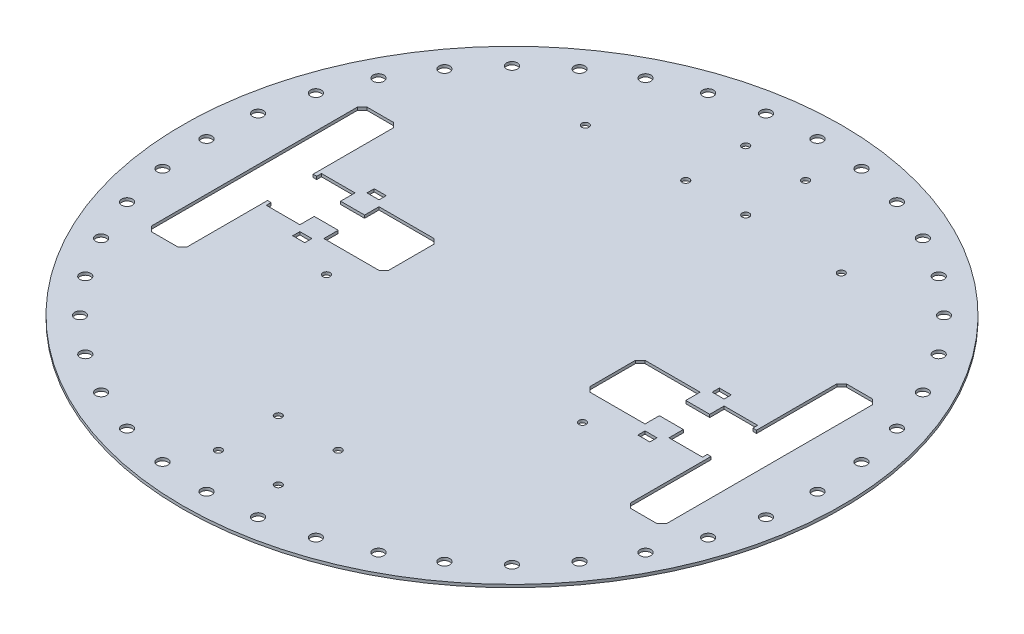
SolidWorks part; units mm, degrees
ref_plane "Front Plane" through (0, 0, 0) normal (0, 0, 1) x (1, 0, 0)
ref_plane "Top Plane" through (0, 0, 0) normal (0, 1, 0) x (1, 0, 0)
ref_plane "Right Plane" through (0, 0, 0) normal (1, 0, 0) x (0, 0, -1)
sketch "Sketch1" plane through (0, 0, 0) normal (0, 1, 0) x (1, 0, 0)
  circle A0 centre (0, 0) radius 137.5
  dimension "D1" = 275
extrude "Boss-Extrude1" add sketch "Sketch1" along normal blind 1.2
sketch "Sketch3" plane through (0, 1.2, 0) normal (0, 1, 0) x (1, 0, 0)
  line L0 (0, 127.4549) -> (0, 0) construction
  line L1 (0, 0) -> (19.9383, 125.8858) construction
  line L2 (39.3857, 121.2169) -> (0, 0) construction
  circle A0 centre (0, 127.4549) radius 2.25
  circle A2 centre (19.9383, 125.8858) radius 2.25
  circle A3 centre (39.3857, 121.2169) radius 2.25
  circle A4 centre (57.8633, 113.5632) radius 2.25
  circle A5 centre (74.9161, 103.1132) radius 2.25
  circle A6 centre (90.1243, 90.1243) radius 2.25
  circle A7 centre (103.1132, 74.9161) radius 2.25
  circle A8 centre (113.5632, 57.8633) radius 2.25
  circle A9 centre (121.2169, 39.3857) radius 2.25
  circle A10 centre (125.8858, 19.9383) radius 2.25
  circle A11 centre (127.4549, 0) radius 2.25
  circle A12 centre (125.8858, -19.9383) radius 2.25
  circle A13 centre (121.2169, -39.3857) radius 2.25
  circle A14 centre (113.5632, -57.8633) radius 2.25
  circle A15 centre (103.1132, -74.9161) radius 2.25
  circle A16 centre (90.1243, -90.1243) radius 2.25
  circle A17 centre (74.9161, -103.1132) radius 2.25
  circle A18 centre (57.8633, -113.5632) radius 2.25
  circle A19 centre (39.3857, -121.2169) radius 2.25
  circle A20 centre (19.9383, -125.8858) radius 2.25
  circle A21 centre (0, -127.4549) radius 2.25
  circle A22 centre (-19.9383, -125.8858) radius 2.25
  circle A23 centre (-39.3857, -121.2169) radius 2.25
  circle A24 centre (-57.8633, -113.5632) radius 2.25
  circle A25 centre (-74.9161, -103.1132) radius 2.25
  circle A26 centre (-90.1243, -90.1243) radius 2.25
  circle A27 centre (-103.1132, -74.9161) radius 2.25
  circle A28 centre (-113.5632, -57.8633) radius 2.25
  circle A29 centre (-121.2169, -39.3857) radius 2.25
  circle A30 centre (-125.8858, -19.9383) radius 2.25
  circle A31 centre (-127.4549, 0) radius 2.25
  circle A32 centre (-125.8858, 19.9383) radius 2.25
  circle A33 centre (-121.2169, 39.3857) radius 2.25
  circle A34 centre (-113.5632, 57.8633) radius 2.25
  circle A35 centre (-103.1132, 74.9161) radius 2.25
  circle A36 centre (-90.1243, 90.1243) radius 2.25
  circle A37 centre (-74.9161, 103.1132) radius 2.25
  circle A38 centre (-57.8633, 113.5632) radius 2.25
  circle A39 centre (-39.3857, 121.2169) radius 2.25
  circle A40 centre (-19.9383, 125.8858) radius 2.25
  dimension "D1" = 4.5
  dimension "D2" = 40
  dimension "D3" = 20
extrude "Cut-Extrude1" cut sketch "Sketch3" against normal through all
sketch "Sketch4" plane through (0, 1.2, 0) normal (0, 1, 0) x (1, 0, 0)
  line L0 (0, 137.5) -> (0, -137.5) construction
  line L1 (-137.5, 0) -> (137.5, 0) construction
  line L2 (-107.5, -43) -> (-107.5, 43)
  line L3 (-105.5, 45) -> (-94.5, 45)
  line L4 (-92.5, 43) -> (-92.5, 9.5)
  line L5 (-92.5, 9.5) -> (-91, 9.5)
  line L6 (-91, 9.5) -> (-91, 11.5)
  line L7 (-91, 11.5) -> (-77, 11.5)
  line L8 (-77, 11.5) -> (-77, 5.5)
  line L9 (-77, 5.5) -> (-67, 5.5)
  line L10 (-67, 5.5) -> (-67, 11.5)
  line L11 (-67, 11.5) -> (-44, 11.5)
  line L12 (-42, 9.5) -> (-42, -9.5)
  line L13 (-67, -11.5) -> (-44, -11.5)
  line L14 (-67, -5.5) -> (-67, -11.5)
  line L15 (-77, -5.5) -> (-67, -5.5)
  line L16 (-77, -11.5) -> (-77, -5.5)
  line L17 (-91, -11.5) -> (-77, -11.5)
  line L18 (-91, -9.5) -> (-91, -11.5)
  line L19 (-92.5, -9.5) -> (-91, -9.5)
  line L20 (-92.5, -43) -> (-92.5, -9.5)
  line L21 (-105.5, -45) -> (-94.5, -45)
  line L22 (-44, 11.5) -> (-42, 9.5)
  line L23 (-44, -11.5) -> (-42, -9.5)
  line L24 (-107.5, 43) -> (-105.5, 45)
  line L25 (-94.5, 45) -> (-92.5, 43)
  line L26 (-107.5, -43) -> (-105.5, -45)
  line L27 (-94.5, -45) -> (-92.5, -43)
  line L28 (94.5, -45) -> (92.5, -43)
  line L29 (107.5, -43) -> (105.5, -45)
  line L30 (94.5, 45) -> (92.5, 43)
  line L31 (107.5, 43) -> (105.5, 45)
  line L32 (44, -11.5) -> (42, -9.5)
  line L33 (44, 11.5) -> (42, 9.5)
  line L34 (105.5, -45) -> (94.5, -45)
  line L35 (92.5, -43) -> (92.5, -9.5)
  line L36 (92.5, -9.5) -> (91, -9.5)
  line L37 (91, -9.5) -> (91, -11.5)
  line L38 (91, -11.5) -> (77, -11.5)
  line L39 (77, -11.5) -> (77, -5.5)
  line L40 (77, -5.5) -> (67, -5.5)
  line L41 (67, -5.5) -> (67, -11.5)
  line L42 (67, -11.5) -> (44, -11.5)
  line L43 (42, 9.5) -> (42, -9.5)
  line L44 (67, 11.5) -> (44, 11.5)
  line L45 (67, 5.5) -> (67, 11.5)
  line L46 (77, 5.5) -> (67, 5.5)
  line L47 (77, 11.5) -> (77, 5.5)
  line L48 (91, 11.5) -> (77, 11.5)
  line L49 (91, 9.5) -> (91, 11.5)
  line L50 (92.5, 9.5) -> (91, 9.5)
  line L51 (92.5, 43) -> (92.5, 9.5)
  line L52 (105.5, 45) -> (94.5, 45)
  line L53 (107.5, -43) -> (107.5, 43)
  circle A2 centre (0, 0) radius 137.5 construction
  point P8 (-107.5, 45)
  point P9 (-42, -11.5)
  point P10 (-92.5, 45)
  point P18 (-42, 11.5)
  point P27 (-92.5, -45)
  point P28 (-107.5, -45)
  point P29 (-100, 0)
  point P39 (-100, 45)
  point P68 (100, 0)
  point P69 (107.5, -45)
  point P70 (92.5, -45)
  point P71 (42, 11.5)
  point P72 (92.5, 45)
  point P73 (42, -11.5)
  point P74 (107.5, 45)
  dimension "D1" = 90
  dimension "D2" = 15
  dimension "D3" = 100
  dimension "D4" = 1.5
  dimension "D5" = 2
  dimension "D6" = 14
  dimension "D7" = 23
  dimension "D8" = 6
  dimension "D9" = 10
  dimension "D10" = 35
extrude "Cut-Extrude2" cut sketch "Sketch4" against normal blind 1.2
sketch "Sketch5" plane through (0, 1.2, 0) normal (0, 1, 0) x (1, 0, 0)
  line L0 (0, 30) -> (0, 0) construction
  line L1 (-53.4, 84) -> (53.4, 84) construction
  line L2 (-53.4, 84) -> (-53.4, -24) construction
  line L3 (-53.4, -24) -> (53.4, -24) construction
  line L4 (53.4, 84) -> (53.4, -24) construction
  line L5 (-53.4, 84) -> (53.4, -24) construction
  line L6 (-53.4, -24) -> (53.4, 84) construction
  circle A0 centre (-53.4, 84) radius 1.5
  circle A1 centre (53.4, 84) radius 1.5
  circle A2 centre (53.4, -24) radius 1.5
  circle A3 centre (-53.4, -24) radius 1.5
  point P0 (0, 30)
  dimension "D3" = 3
  dimension "D1" = 106.8
  dimension "D2" = 108
  dimension "D4" = 30
extrude "Cut-Extrude3" cut sketch "Sketch5" against normal through all
sketch "Sketch6" plane through (0, 1.2, 0) normal (0, 1, 0) x (1, 0, 0)
  line L0 (-137.5, 0) -> (137.5, 0) construction
  line L1 (0, 137.5) -> (0, -137.5) construction
  line L2 (-12.5, -85) -> (12.5, -110) construction
  line L3 (-12.5, 110) -> (12.5, 110) construction
  line L4 (-12.5, 110) -> (-12.5, 85) construction
  line L5 (-12.5, 85) -> (12.5, 85) construction
  line L6 (12.5, 110) -> (12.5, 85) construction
  line L7 (-12.5, 110) -> (12.5, 85) construction
  line L8 (-12.5, 85) -> (12.5, 110) construction
  line L9 (-12.5, -110) -> (12.5, -85) construction
  line L10 (12.5, -110) -> (12.5, -85) construction
  line L11 (-12.5, -85) -> (12.5, -85) construction
  line L12 (-12.5, -110) -> (-12.5, -85) construction
  line L13 (-12.5, -110) -> (12.5, -110) construction
  circle A0 centre (0, 0) radius 137.5 construction
  circle A1 centre (-12.5, 110) radius 1.5
  circle A2 centre (12.5, 110) radius 1.5
  circle A3 centre (12.5, 85) radius 1.5
  circle A4 centre (-12.5, 85) radius 1.5
  circle A5 centre (-12.5, -85) radius 1.5
  circle A6 centre (12.5, -85) radius 1.5
  circle A7 centre (12.5, -110) radius 1.5
  circle A8 centre (-12.5, -110) radius 1.5
  point P7 (0, 97.5)
  point P24 (0, -97.5)
  dimension "D1" = 3
  dimension "D2" = 25
  dimension "D3" = 40
extrude "Cut-Extrude4" cut sketch "Sketch6" against normal through all
sketch "Sketch7" plane through (0, 1.2, 0) normal (0, 1, 0) x (1, 0, 0)
  line L0 (-137.5, 0) -> (137.5, 0) construction
  line L1 (0, 137.5) -> (0, -137.5) construction
  line L2 (-67, 5.5) -> (-77, 5.5) construction
  line L3 (-74.5, 17) -> (-69.5, 17)
  line L4 (-74.5, 17) -> (-74.5, 14)
  line L5 (-74.5, 14) -> (-69.5, 14)
  line L6 (-69.5, 17) -> (-69.5, 14)
  line L7 (-74.5, 17) -> (-69.5, 14) construction
  line L8 (-74.5, 14) -> (-69.5, 17) construction
  line L9 (-74.5, -14) -> (-69.5, -17) construction
  line L10 (-74.5, -17) -> (-69.5, -14) construction
  line L11 (-69.5, -17) -> (-69.5, -14)
  line L12 (-74.5, -14) -> (-69.5, -14)
  line L13 (-74.5, -17) -> (-74.5, -14)
  line L14 (-74.5, -17) -> (-69.5, -17)
  line L15 (74.5, -17) -> (69.5, -14) construction
  line L16 (74.5, -14) -> (69.5, -17) construction
  line L17 (74.5, 14) -> (69.5, 17) construction
  line L18 (74.5, 17) -> (69.5, 14) construction
  line L19 (74.5, -17) -> (69.5, -17)
  line L20 (74.5, -17) -> (74.5, -14)
  line L21 (74.5, -14) -> (69.5, -14)
  line L22 (69.5, -17) -> (69.5, -14)
  line L23 (69.5, 17) -> (69.5, 14)
  line L24 (74.5, 14) -> (69.5, 14)
  line L25 (74.5, 17) -> (74.5, 14)
  line L26 (74.5, 17) -> (69.5, 17)
  circle A0 centre (0, 0) radius 137.5 construction
  point P8 (-72, 15.5)
  point P15 (-72, 5.5)
  point P20 (-72, -15.5)
  point P29 (72, -15.5)
  point P30 (72, 15.5)
  dimension "D1" = 5
  dimension "D2" = 3
  dimension "D3" = 10
extrude "Cut-Extrude5" cut sketch "Sketch7" against normal through all
